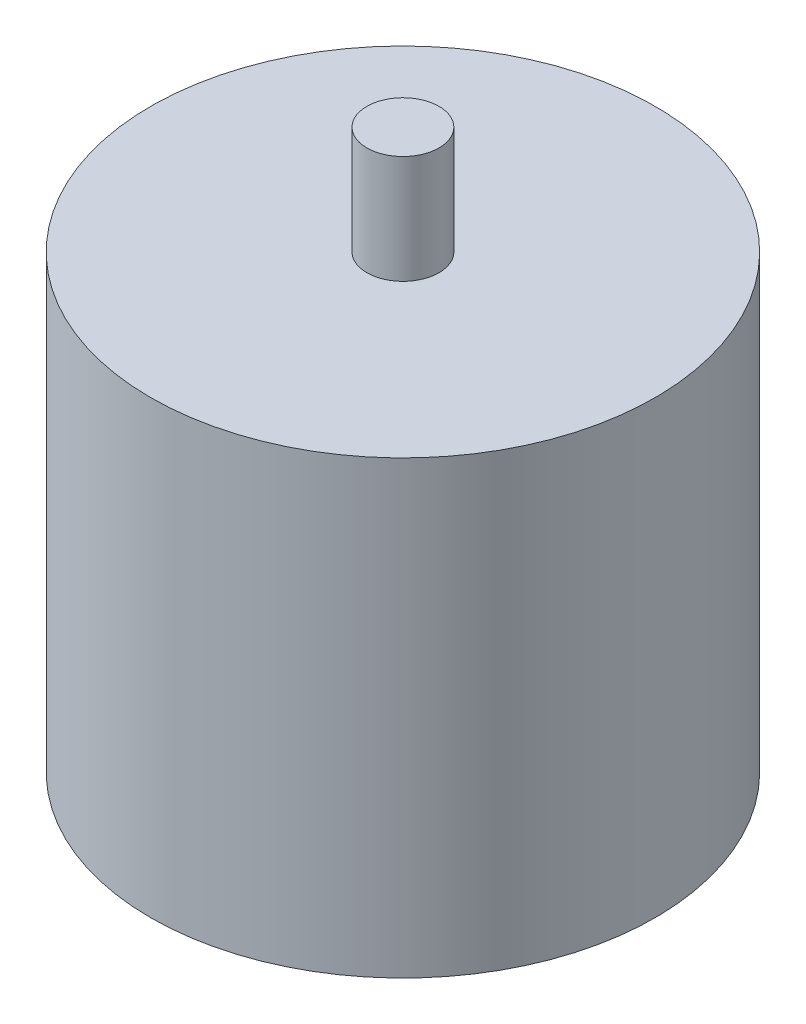
SolidWorks part; units mm, degrees
ref_plane "Front Plane" through (0, 0, 0) normal (0, 0, 1) x (1, 0, 0)
ref_plane "Top Plane" through (0, 0, 0) normal (0, 1, 0) x (1, 0, 0)
ref_plane "Right Plane" through (0, 0, 0) normal (1, 0, 0) x (0, 0, -1)
sketch "Sketch1" plane through (0, 0, 0) normal (0, 1, 0) x (1, 0, 0)
  circle A0 centre (0, 0) radius 14
  dimension "D1" = 28
extrude "Boss-Extrude1" add sketch "Sketch1" along normal blind 25
sketch "Sketch2" plane through (0, 25, 0) normal (0, 1, 0) x (1, 0, 0)
  circle A0 centre (0, 0) radius 2
extrude "Boss-Extrude2" add sketch "Sketch2" along normal blind 6
